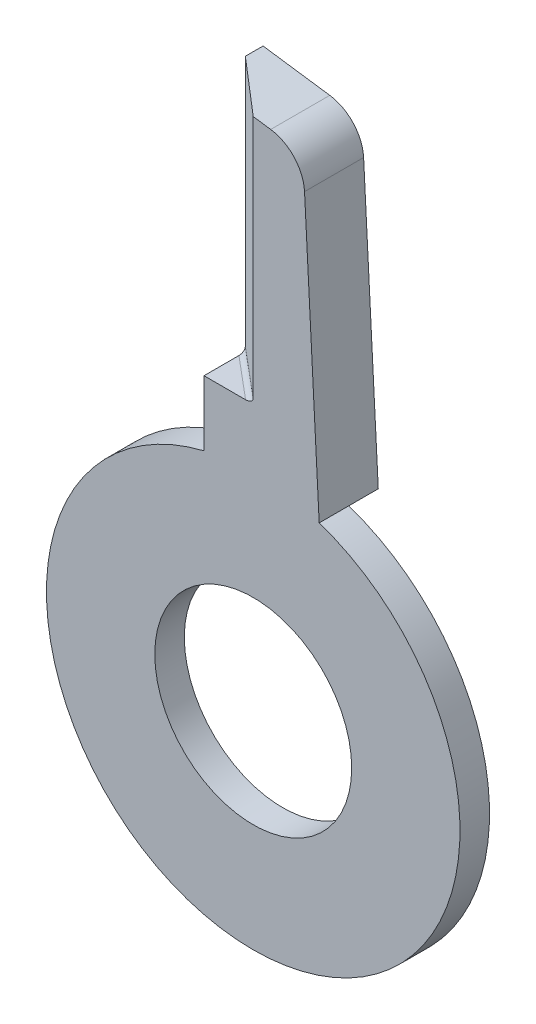
SolidWorks part; units mm, degrees
ref_plane "Alzado" through (0, 0, 0) normal (0, 0, 1) x (1, 0, 0)
ref_plane "Planta" through (0, 0, 0) normal (0, 1, 0) x (1, 0, 0)
ref_plane "Vista lateral" through (0, 0, 0) normal (1, 0, 0) x (0, 0, -1)
sketch "Croquis1" plane through (0, 0, 0) normal (0, 0, 1) x (1, 0, 0)
  line L0 (0, 94.0827) -> (0, -21) construction
  line L1 (-21, 0) -> (21, 0) construction
  line L2 (-5, 20.3961) -> (-5, 53)
  line L3 (-5, 53) -> (1.7741, 52.048)
  line L4 (5.2119, 48.2962) -> (6.7, 19.9025)
  arc A0 (-5, 20.3961) -> (6.7, 19.9025) centre (0, 0) ccw
  circle A1 centre (0, 0) radius 10
  arc A2 (1.7741, 52.048) -> (5.2119, 48.2962) centre (1.2174, 48.0869) cw
  dimension "D1" = 20
  dimension "D2" = 42
  dimension "D8" = 4
  dimension "D3" = 5
  dimension "D4" = 98
  dimension "D5" = 3
  dimension "D6" = 74
  dimension "D7" = 11.7
extrude "Saliente-Extruir1" add sketch "Croquis1" along normal blind 6
sketch "Croquis2" plane through (0, 0, 0) normal (0, 0, -1) x (-1, 0, 0)
  circle A0 centre (0, 0) radius 21
  circle A1 centre (0, 0) radius 10
  circle A2 centre (0, 0) radius 10 construction
  arc A3 (-6.7, 19.9025) -> (5, 20.3961) centre (0, 0) ccw construction
extrude "Cortar-Extruir1" cut sketch "Croquis2" against normal blind 3
ref_plane "Plano1" through (0, 53, 0) normal (0, 1, 0) x (-1, 0, 0)
sketch "Croquis3" plane through (0, 53, 0) normal (0, 1, 0) x (-1, 0, 0)
  line L0 (5, 6) -> (5, 1.8)
  line L1 (5, 6) -> (5, 0) construction
  line L2 (5, 1.8) -> (0, 6)
  line L3 (0, 6) -> (5, 6)
  dimension "D1" = 5
  dimension "D2" = 1.8
  dimension "D3" = 40.03
extrude "Cortar-Extruir2" cut sketch "Croquis3" against normal blind 26
fillet "Redondeo1" radius 0.5 1 edges at (-2.5, 27, 3.9)
